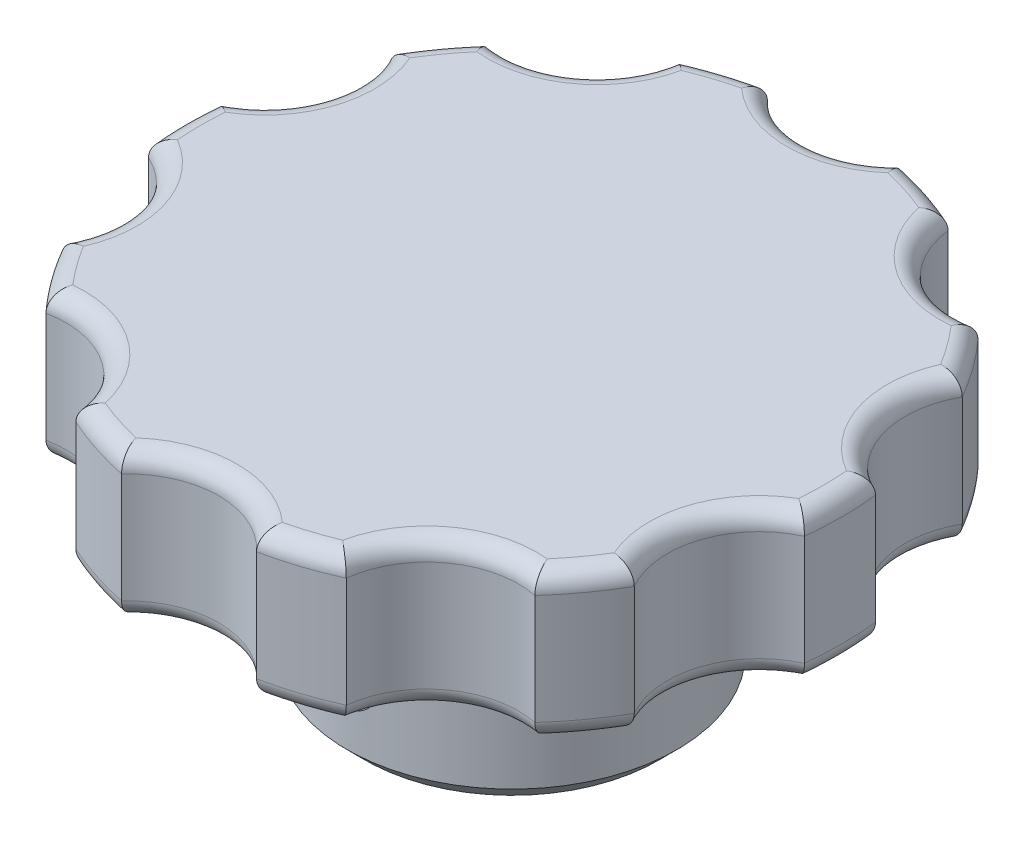
SolidWorks part; units mm, degrees
material "Nylon 101"
ref_plane "Front Plane" through (0, 0, 0) normal (0, 0, 1) x (1, 0, 0)
ref_plane "Top Plane" through (0, 0, 0) normal (0, 1, 0) x (1, 0, 0)
ref_plane "Right Plane" through (0, 0, 0) normal (1, 0, 0) x (0, 0, -1)
sketch "Sketch1" plane through (0, 0, 0) normal (0, 0, 1) x (1, 0, 0)
  line L0 (0, 38.8868) -> (0, -39.1132) construction
  line L1 (-6, 0) -> (-6, 14)
  line L2 (-6, 14) -> (0, 14)
  line L3 (0, 14) -> (0, 17.5)
  line L4 (0, 17.5) -> (-18, 17.5)
  line L5 (-18, 17.5) -> (-18, 9.5)
  line L6 (-18, 9.5) -> (-9, 9.5)
  line L7 (-9, 9.5) -> (-9, 0)
  line L8 (-9, 0) -> (-6, 0)
  line L9 (-32.8868, 0) -> (19.7547, 0) construction
  dimension "D1" = 18
  dimension "D2" = 9.5
  dimension "D3" = 14
  dimension "D4" = 8
  dimension "D5" = 36
  dimension "D6" = 12
revolve "Revolve1" add sketch "Sketch1" angle 360 about L0
sketch "Sketch2" plane through (0, 17.5, 0) normal (0, 1, 0) x (1, 0, 0)
  line L0 (-5, 21) -> (5, 21)
  arc A0 (-5, 21) -> (5, 21) centre (0, 21) ccw
  circle A3 centre (0, 0) radius 18 construction
  point P5 (0, 16)
  point P6 (0, 18)
  dimension "D1" = 2
  dimension "D2" = 5
  dimension "D3" = 10
extrude "Cut-Extrude1" cut sketch "Sketch2" against normal through all
pattern_circular "CirPattern1" count 10 over 360 about axis through (0, 0, 0) along (0, 1, 0) of "Cut-Extrude1"
fillet "Fillet1" radius 1 41 edges at (0, 9.5, 9) (-18, 9.5, 0) (-14.5623, 9.5, -10.5801) (-15.2169, 9.5, 4.9443) (-14.5623, 9.5, 10.5801) (0, 9.5, -16) (-5.5623, 9.5, -17.119) (-9.4046, 9.5, -12.9443) (-15.2169, 9.5, -4.9443) (-5.5623, 17.5, -17.119) (-14.5623, 17.5, -10.5801) (-9.4046, 17.5, -12.9443) (0, 17.5, -16) (-18, 17.5, 0) (-14.5623, 17.5, 10.5801) (-15.2169, 17.5, 4.9443) (-15.2169, 17.5, -4.9443) (14.5623, 9.5, -10.5801) (5.5623, 9.5, -17.119) (-9.4046, 9.5, 12.9443) (-5.5623, 9.5, 17.119) (0, 9.5, 16) (5.5623, 9.5, 17.119) (9.4046, 9.5, 12.9443) (14.5623, 9.5, 10.5801) (15.2169, 9.5, 4.9443) (18, 9.5, 0) (15.2169, 9.5, -4.9443) (9.4046, 9.5, -12.9443) (18, 17.5, 0) (14.5623, 17.5, -10.5801) (15.2169, 17.5, -4.9443) (14.5623, 17.5, 10.5801) (15.2169, 17.5, 4.9443) (5.5623, 17.5, 17.119) (9.4046, 17.5, 12.9443) (-5.5623, 17.5, 17.119) (0, 17.5, 16) (-9.4046, 17.5, 12.9443) (5.5623, 17.5, -17.119) (9.4046, 17.5, -12.9443)
chamfer "Chamfer1" distance 1 angle 45 1 edges at (0, 0, 9)
ref_plane "Plane1" through (0, 0, 9) normal (0, 0, 1) x (1, 0, 0)
sketch "Sketch4" plane through (0, 0, 9) normal (0, 0, 1) x (1, 0, 0)
  line L0 (0, 0) -> (0, 14) construction
  line L1 (-8, 0) -> (8, 0) construction
  line L2 (-8, 0) -> (8, 0) construction
  circle A0 centre (0, 4.5) radius 1.5
  dimension "D2" = 3
  dimension "D1" = 4.5
extrude "Cut-Extrude2" cut sketch "Sketch4" against normal blind 10
equation "\"A\"= 8"
equation "\"B\"= 36"
equation "\"C\"= 14"
equation "\"D3@Sketch1\"=\"C\""
equation "\"D4@Sketch1\"=\"A\""
equation "\"D5@Sketch1\"=\"B\""
